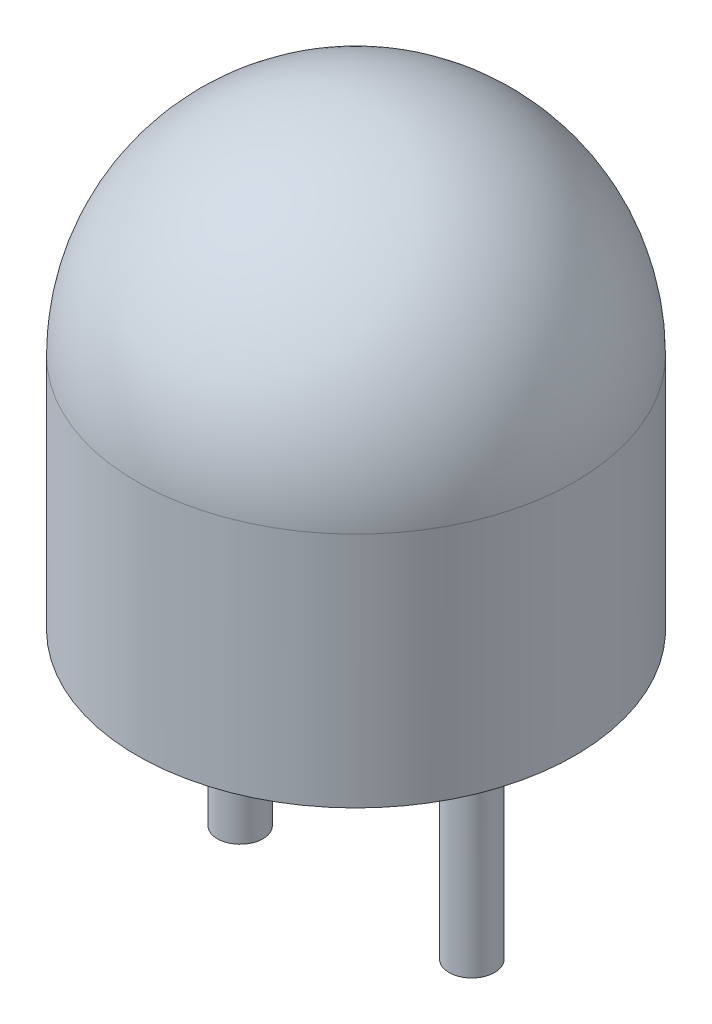
SolidWorks part; units mm, degrees
ref_plane "Plan de face" through (0, 0, 0) normal (0, 0, 1) x (1, 0, 0)
ref_plane "Plan de dessus" through (0, 0, 0) normal (0, 1, 0) x (1, 0, 0)
ref_plane "Plan de droite" through (0, 0, 0) normal (1, 0, 0) x (0, 0, -1)
sketch "Esquisse1" plane through (0, 0, 0) normal (0, 1, 0) x (1, 0, 0)
  line L0 (-1.27, 0) -> (1.27, 0) construction
  circle A0 centre (1.27, 0) radius 0.25
  circle A1 centre (-1.27, 0) radius 0.25
  dimension "D2" = 0.5
  dimension "D1" = 2.54
extrude "Boss.-Extru.1" add sketch "Esquisse1" against normal blind 2.5
sketch "Esquisse2" plane through (0, 0, 0) normal (0, 0, 1) x (1, 0, 0)
  line L0 (1.52, 0) -> (1.52, 3)
  line L1 (1.52, 3) -> (-1.02, 3)
  line L2 (-1.02, 3) -> (0, 1.3)
  line L3 (1.02, 0.7225) -> (1.02, 0)
  line L4 (1.02, 0) -> (1.52, 0)
  line L5 (-1.52, 0) -> (-1.52, 3)
  line L6 (-1.52, 3) -> (-0.5, 1.3)
  line L7 (-0.5, 1.3) -> (-1.02, 1.3)
  line L8 (-1.02, 1.3) -> (-1.02, 0)
  line L9 (-1.02, 0) -> (-1.52, 0)
  arc A0 (0, 1.3) -> (1.02, 0.7225) centre (1.02, 1.912) ccw
  dimension "D1" = 3
  dimension "D2" = 1.3
extrude "Boss.-Extru.2" add sketch "Esquisse2" along normal mid plane 0.2
sketch "Esquisse4" plane through (0, 0, 0) normal (0, 0, 1) x (1, 0, 0)
  line L0 (0, 3) -> (0.5, 3)
  line L1 (1.52, 3) -> (-1.02, 3) construction
  line L2 (0.5, 3) -> (0, 2.5)
  line L3 (0, 2.5) -> (0, 3)
revolve "Révolution1" add sketch "Esquisse4" angle 360 about L3
sketch "Esquisse5" plane through (0, 0, 0) normal (0, 0, 1) x (1, 0, 0)
  line L0 (0, 0) -> (0, 5)
  line L1 (0, 0) -> (2.4, 0)
  line L2 (2.4, 0) -> (2.4, 2.6)
  arc A0 (2.4, 2.6) -> (0, 5) centre (0, 2.6) ccw
  dimension "D1" = 5
  dimension "D2" = 2.4
revolve "Révolution2" add sketch "Esquisse5" angle 360 about L0
